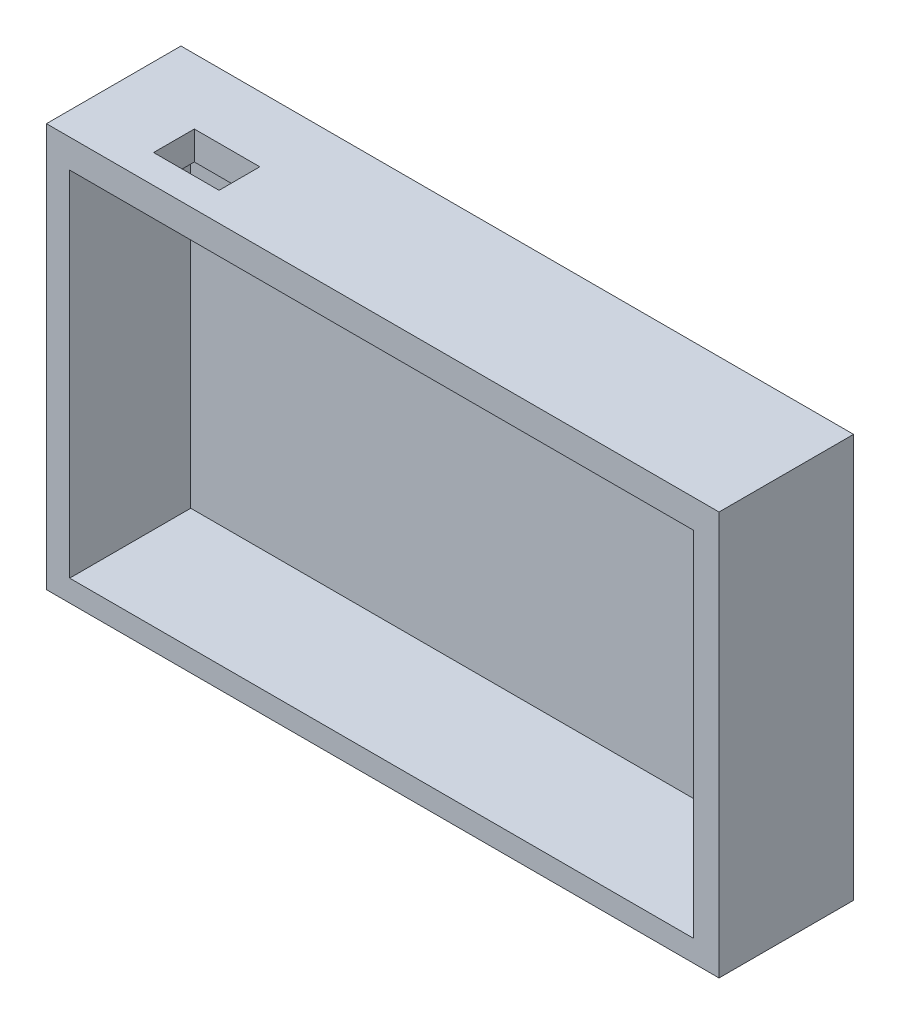
SolidWorks part; units mm, degrees
material "ABS PC"
ref_plane "Front Plane" through (0, 0, 0) normal (0, 0, 1) x (1, 0, 0)
ref_plane "Top Plane" through (0, 0, 0) normal (0, 1, 0) x (1, 0, 0)
ref_plane "Right Plane" through (0, 0, 0) normal (1, 0, 0) x (0, 0, -1)
sketch "Sketch1" plane through (0, 0, 0) normal (0, 0, 1) x (1, 0, 0)
  line L1 (-44.2105, 23.1579) -> (55.7895, 23.1579)
  line L2 (-44.2105, 23.1579) -> (-44.2105, -36.8421)
  line L3 (-44.2105, -36.8421) -> (55.7895, -36.8421)
  line L4 (55.7895, 23.1579) -> (55.7895, -36.8421)
  dimension "D1" = 100
  dimension "D2" = 60
extrude "Boss-Extrude2" add sketch "Sketch1" along normal blind 20
sketch "Sketch3" plane through (0, 0, 20) normal (0, 0, 1) x (1, 0, 0)
  line L1 (-40.7553, 18.9127) -> (52.0239, 18.9127)
  line L2 (-40.7553, 18.9127) -> (-40.7553, -33.6312)
  line L3 (-40.7553, -33.6312) -> (52.0239, -33.6312)
  line L4 (52.0239, 18.9127) -> (52.0239, -33.6312)
extrude "Cut-Extrude2" cut sketch "Sketch3" against normal blind 18
sketch "Sketch5" plane through (0, 23.1579, 0) normal (0, 1, 0) x (1, 0, 0)
  line L0 (-22.7949, -9.6909) -> (-32.5301, -9.6909)
  line L3 (-32.5301, -9.6909) -> (-32.5301, -15.7492)
  line L4 (-32.5301, -15.7492) -> (-22.7949, -15.7492)
  line L5 (-22.7949, -15.7492) -> (-22.7949, -9.6909)
extrude "Cut-Extrude3" cut sketch "Sketch5" against normal blind 10
